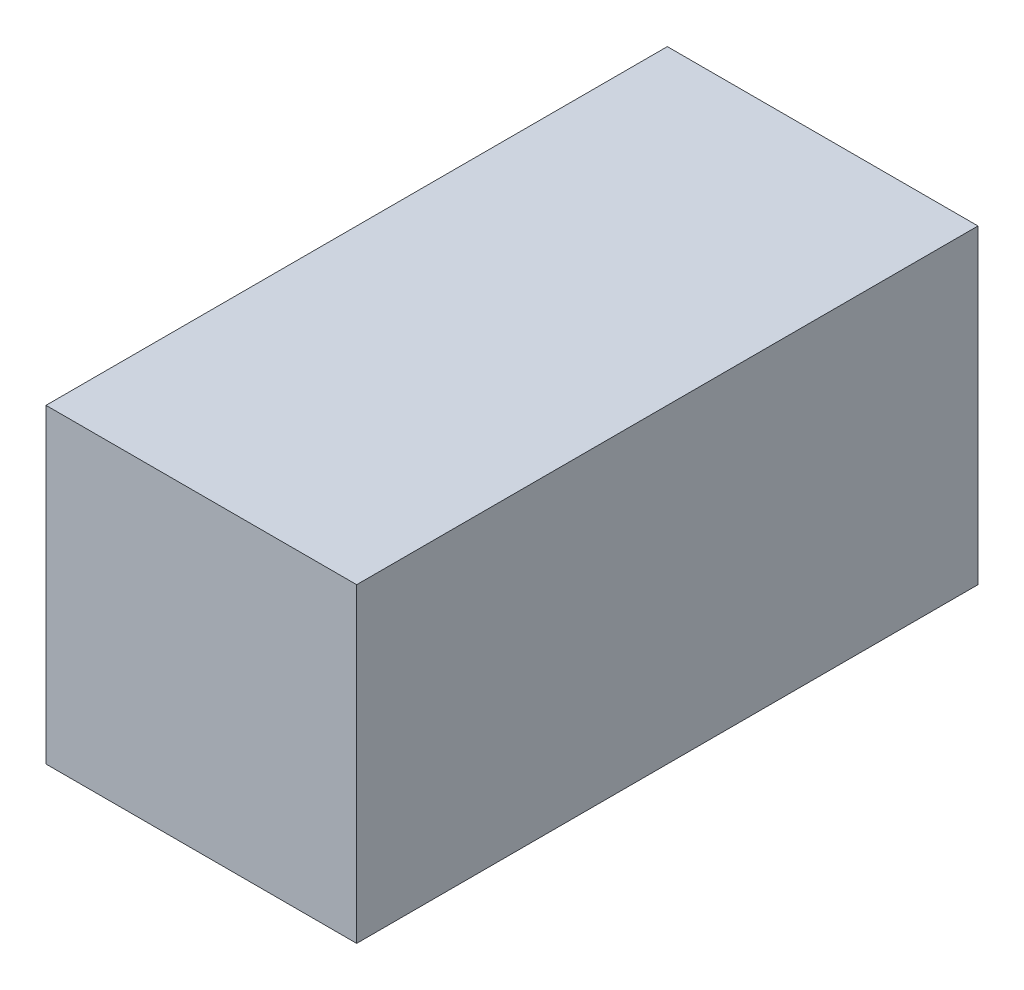
SolidWorks part; units mm, degrees
ref_plane "Alzado" through (0, 0, 0) normal (0, 0, 1) x (1, 0, 0)
ref_plane "Planta" through (0, 0, 0) normal (0, 1, 0) x (1, 0, 0)
ref_plane "Vista lateral" through (0, 0, 0) normal (1, 0, 0) x (0, 0, -1)
sketch "Croquis1" plane through (0, 0, 0) normal (0, 0, 1) x (1, 0, 0)
  line L1 (23.3243, 23.3243) -> (-6.6757, 23.3243)
  line L2 (23.3243, 23.3243) -> (23.3243, -6.6757)
  line L3 (23.3243, -6.6757) -> (-6.6757, -6.6757)
  line L4 (-6.6757, 23.3243) -> (-6.6757, -6.6757)
  dimension "D1" = 30
  dimension "D2" = 30
extrude "Saliente-Extruir1" add sketch "Croquis1" along normal blind 60
